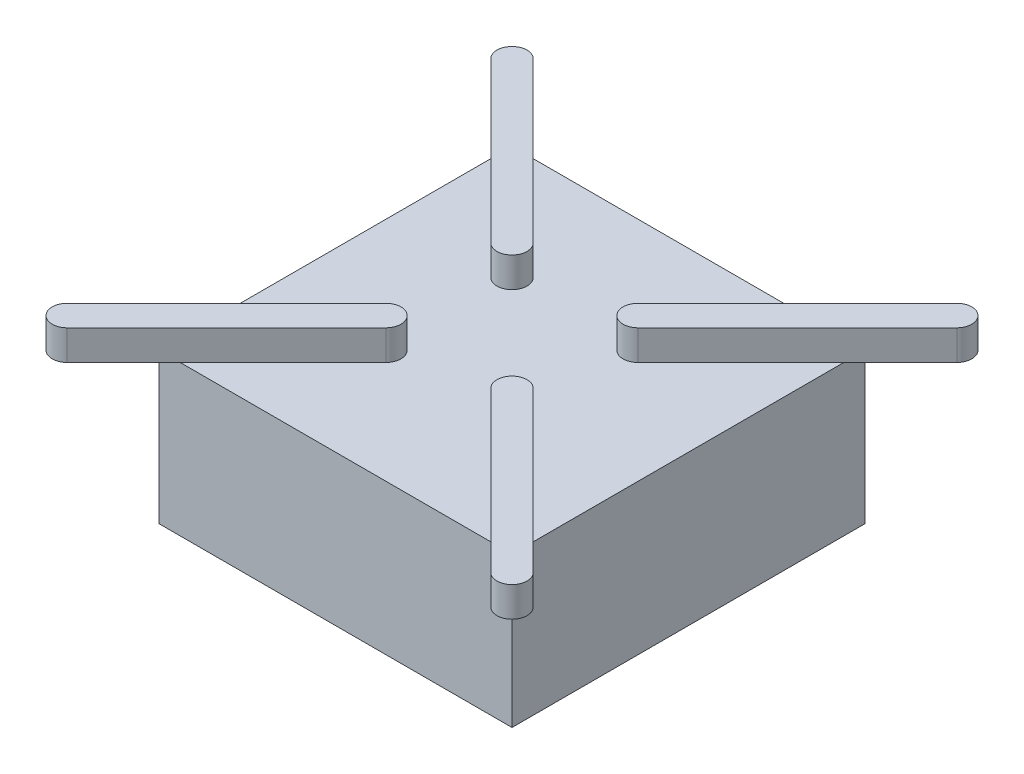
SolidWorks part; units mm, degrees
ref_plane "Plan de face" through (0, 0, 0) normal (0, 0, 1) x (1, 0, 0)
ref_plane "Plan de dessus" through (0, 0, 0) normal (0, 1, 0) x (1, 0, 0)
ref_plane "Plan de droite" through (0, 0, 0) normal (1, 0, 0) x (0, 0, -1)
sketch "Esquisse1" plane through (0, 0, 0) normal (0, 1, 0) x (1, 0, 0)
  line L0 (-23.5, 23.5) -> (23.5, -23.5) construction
  line L1 (-23.5, 23.5) -> (23.5, 23.5)
  line L2 (-23.5, 23.5) -> (-23.5, -23.5)
  line L3 (-23.5, -23.5) -> (23.5, -23.5)
  line L4 (23.5, 23.5) -> (23.5, -23.5)
  dimension "D1" = 47
extrude "Boss.-Extru.1" add sketch "Esquisse1" along normal blind 20
sketch "Esquisse2" plane through (0, 0, 0) normal (0, -1, 0) x (1, 0, 0)
  line L0 (0, 0) -> (0, -35.6209) construction
  line L1 (0, 0) -> (23.5, 0) construction
  circle A0 centre (19, -19) radius 1
  circle A1 centre (-19, -19) radius 1
  circle A2 centre (-19, 19) radius 1
  circle A3 centre (19, 19) radius 1
  dimension "D1" = 2
  dimension "D2" = 38
  dimension "D3" = 38
extrude "Boss.-Extru.2" add sketch "Esquisse2" along normal blind 3
sketch "Esquisse3" plane through (0, 20, 0) normal (0, 1, 0) x (1, 0, 0)
  line L0 (8.3934, -8.3934) -> (29.6066, -29.6066) construction
  line L1 (9.8076, -6.9792) -> (31.0208, -28.1924)
  line L2 (6.9792, -9.8076) -> (28.1924, -31.0208)
  line L3 (0, 0) -> (46.1617, 0) construction
  line L4 (0, 0) -> (0, 52.6319) construction
  line L5 (8.3934, 8.3934) -> (29.6066, 29.6066) construction
  line L6 (9.8076, 6.9792) -> (31.0208, 28.1924)
  line L7 (6.9792, 9.8076) -> (28.1924, 31.0208)
  line L8 (-8.3934, -8.3934) -> (-29.6066, -29.6066) construction
  line L9 (-9.8076, -6.9792) -> (-31.0208, -28.1924)
  line L10 (-6.9792, -9.8076) -> (-28.1924, -31.0208)
  line L11 (-8.3934, 8.3934) -> (-29.6066, 29.6066) construction
  line L12 (-9.8076, 6.9792) -> (-31.0208, 28.1924)
  line L13 (-6.9792, 9.8076) -> (-28.1924, 31.0208)
  arc A0 (9.8076, -6.9792) -> (6.9792, -9.8076) centre (8.3934, -8.3934) ccw
  arc A1 (28.1924, -31.0208) -> (31.0208, -28.1924) centre (29.6066, -29.6066) ccw
  circle A2 centre (19, -19) radius 1 construction
  arc A3 (9.8076, 6.9792) -> (6.9792, 9.8076) centre (8.3934, 8.3934) cw
  arc A4 (28.1924, 31.0208) -> (31.0208, 28.1924) centre (29.6066, 29.6066) cw
  arc A5 (-9.8076, -6.9792) -> (-6.9792, -9.8076) centre (-8.3934, -8.3934) cw
  arc A6 (-28.1924, -31.0208) -> (-31.0208, -28.1924) centre (-29.6066, -29.6066) cw
  arc A7 (-9.8076, 6.9792) -> (-6.9792, 9.8076) centre (-8.3934, 8.3934) ccw
  arc A8 (-28.1924, 31.0208) -> (-31.0208, 28.1924) centre (-29.6066, 29.6066) ccw
  point P2 (19, -19)
  point P15 (19, 19)
  point P22 (-19, -19)
  point P29 (-19, 19)
  dimension "D1" = 30
  dimension "D2" = 4
extrude "Boss.-Extru.3" add sketch "Esquisse3" along normal blind 4
sketch "Esquisse4" plane through (0, 0, 0) normal (0, -1, 0) x (1, 0, 0)
  line L0 (-13, 13) -> (13, -13) construction
  line L1 (-13, 13) -> (13, 13)
  line L2 (-13, 13) -> (-13, -13)
  line L3 (-13, -13) -> (13, -13)
  line L4 (13, 13) -> (13, -13)
  dimension "D1" = 26
extrude "Boss.-Extru.4" add sketch "Esquisse4" along normal blind 2
